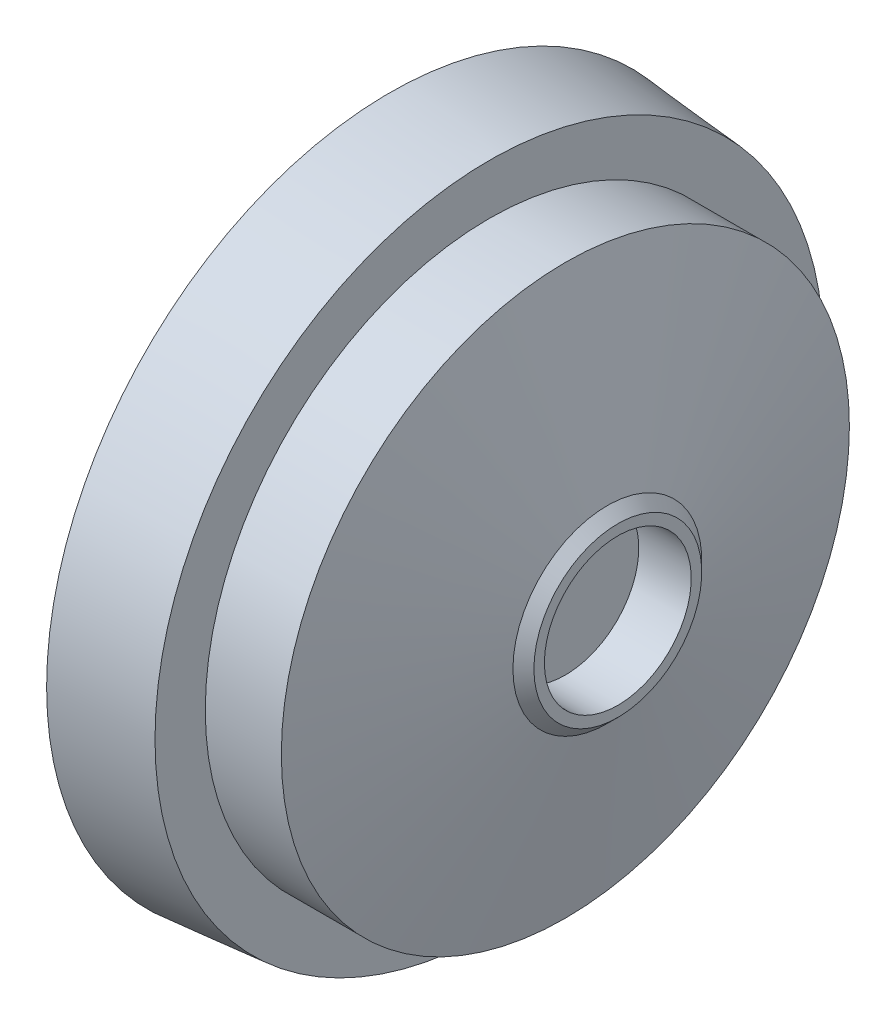
SolidWorks part; units mm, degrees
ref_plane "Front Plane" through (0, 0, 0) normal (0, 0, 1) x (1, 0, 0)
ref_plane "Top Plane" through (0, 0, 0) normal (0, 1, 0) x (1, 0, 0)
ref_plane "Right Plane" through (0, 0, 0) normal (1, 0, 0) x (0, 0, -1)
sketch "Sketch1" plane through (0, 0, 0) normal (0, 0, 1) x (1, 0, 0)
  line L0 (0, 69.4242) -> (0, 0) construction
  line L1 (0, 0) -> (52.1897, 0) construction
  line L2 (0, 65.4) -> (19, 63.7377)
  line L3 (19, 63.7377) -> (19, 54.15)
  line L4 (19, 54.15) -> (33.5, 54.15)
  line L5 (33.5, 54.15) -> (41.5, 18)
  line L6 (41.5, 18) -> (43.5, 16)
  line L7 (43.5, 16) -> (43.5, 14)
  line L8 (41.5, 18) -> (43.2413, 18) construction
  line L9 (43.5, 14) -> (33.5, 14)
  line L10 (33.5, 14) -> (33.5, 0)
  line L11 (33.5, 0) -> (0, 0)
  line L13 (-1.6, 53.6) -> (10.4, 53.6)
  line L14 (10.4, 53.6) -> (10.4, 60.9)
  line L15 (10.4, 60.9) -> (0, 60.9)
  line L16 (0, 60.9) -> (0, 65.4)
  line L17 (0, 0) -> (-1.6, 0)
  line L18 (-1.6, 0) -> (-1.6, 53.6)
  dimension "D1" = 130.8
  dimension "D2" = 108.3
  dimension "D3" = 36
  dimension "D4" = 19
  dimension "D5" = 33.5
  dimension "D6" = 43.5
  dimension "D7" = 2
  dimension "D8" = 85
  dimension "D9" = 45
  dimension "D10" = 2
  dimension "D11" = 4.5
  dimension "D12" = 7.3
  dimension "D13" = 1.6
  dimension "D14" = 12
  dimension "D15" = 10
revolve "Revolve1" add sketch "Sketch1" angle 360 about L1
fillet "Fillet1" radius 3 1 edges at (-1.6, 0, 53.6)
